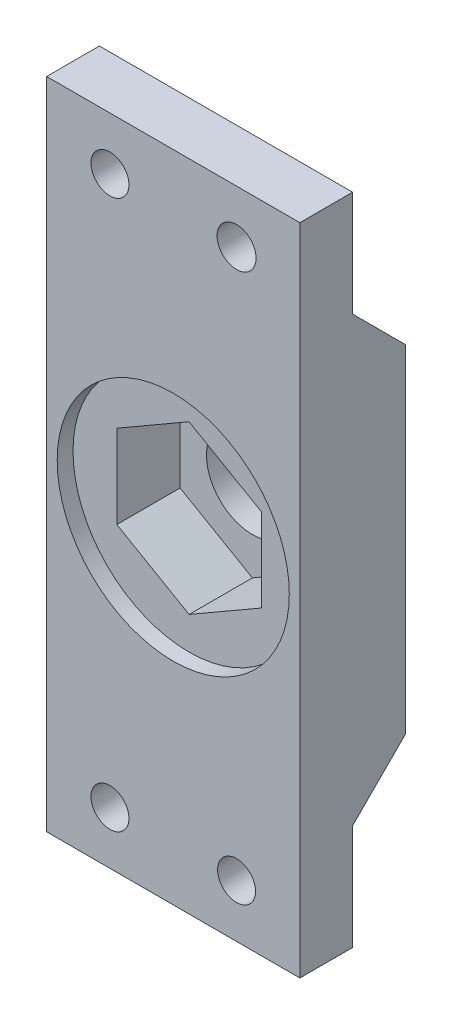
SolidWorks part; units mm, degrees
ref_plane "Plano frontal" through (0, 0, 0) normal (0, 0, 1) x (1, 0, 0)
ref_plane "Plano superior" through (0, 0, 0) normal (0, 1, 0) x (1, 0, 0)
ref_plane "Plano direito" through (0, 0, 0) normal (1, 0, 0) x (0, 0, -1)
sketch "Esboço1" plane through (0, 0, 0) normal (0, 0, 1) x (1, 0, 0)
  line L1 (-12, 31) -> (12, 31)
  line L2 (-12, 31) -> (-12, -31)
  line L3 (-12, -31) -> (12, -31)
  line L4 (12, 31) -> (12, -31)
  line L5 (-12, 31) -> (12, -31) construction
  line L6 (-12, -31) -> (12, 31) construction
  point P0 (0, 0)
extrude "Ressalto-extrusão1" add sketch "Esboço1" along normal blind 10
sketch "Esboço4" plane through (0, 0, 10) normal (0, 0, -1) x (-1, 0, 0)
  circle A0 centre (0, 0) radius 11
extrude "Corte-extrusão1" cut sketch "Esboço4" along normal blind 1.5
sketch "Esboço6" plane through (0, 0, 8.5) normal (0, 0, 1) x (1, 0, 0)
  line L1 (0, -7.9097) -> (6.85, -3.9548)
  line L2 (6.85, -3.9548) -> (6.85, 3.9548)
  line L3 (6.85, 3.9548) -> (0, 7.9097)
  line L4 (0, 7.9097) -> (-6.85, 3.9548)
  line L5 (-6.85, 3.9548) -> (-6.85, -3.9548)
  line L6 (-6.85, -3.9548) -> (0, -7.9097)
  circle A0 centre (0, 0) radius 6.85 construction
extrude "Corte-extrusão2" cut sketch "Esboço6" against normal blind 6
sketch "Esboço9" plane through (0, 0, 10) normal (0, 0, 1) x (1, 0, 0)
  line L0 (0, 31) -> (0, 26) construction
  line L1 (12, 31) -> (-12, 31) construction
  line L2 (0, -31) -> (0, -26) construction
  line L3 (-12, -31) -> (12, -31) construction
  line L4 (0, 26) -> (6, 26) construction
  line L5 (6, 26) -> (-6, 26) construction
  line L6 (-6, 26) -> (-6, -26) construction
  line L7 (-6, -26) -> (6, -26) construction
  circle A0 centre (0, 0) radius 4.35
  circle A1 centre (6, 26) radius 1.85
  circle A2 centre (-6, 26) radius 1.8
  circle A3 centre (-6, -26) radius 1.8
  circle A4 centre (6, -26) radius 1.8
extrude "Corte-extrusão4" cut sketch "Esboço9" against normal through all
sketch "Esboço11" plane through (-12, 0, 0) normal (-1, 0, 0) x (0, 0, 1)
  line L0 (5.0046, -21) -> (5, -31)
  line L1 (0, 31) -> (0, -31) construction
  line L2 (10, -31) -> (0, -31) construction
  line L3 (5, -31) -> (10, -31)
  line L4 (5.0046, -21) -> (0, -15.9954)
  line L5 (0, 15.9954) -> (0, -15.9954)
  line L6 (0, 0) -> (10, 0) construction
  line L8 (10, 31) -> (10, -31)
  line L9 (5.0046, 21) -> (0, 15.9954)
  line L10 (5, 31) -> (10, 31)
  line L11 (5.0046, 21) -> (5, 31)
extrude "Corte-extrusão7" cut sketch "Esboço11" against normal through all flip side to cut
sketch "Esboço12" plane through (0, 0.0023, 5.0141) normal (0, -0.0005, -1) x (-1, 0, 0)
  line L0 (11.7, 21.2977) -> (11.7, 30.6977)
  line L1 (11.7, 30.6977) -> (-11.7, 30.6977)
  line L2 (-11.7, 30.6977) -> (-11.7, 21.2977)
  line L3 (-11.7, 21.2977) -> (11.7, 21.2977)
  line L4 (12, 20.9977) -> (12, 30.9977)
  line L5 (12, 30.9977) -> (-12, 30.9977)
  line L6 (-12, 30.9977) -> (-12, 20.9977)
  line L7 (-12, 20.9977) -> (12, 20.9977)
  line L8 (12, 20.9977) -> (12, 30.9977)
  line L9 (12, 30.9977) -> (-12, 30.9977)
  line L10 (-12, 30.9977) -> (-12, 20.9977)
  line L11 (-12, 20.9977) -> (12, 20.9977)
  line L12 (0, 0) -> (11.7, 0) construction
  line L13 (-12, -20.9977) -> (12, -20.9977)
  line L14 (-12, -30.9977) -> (-12, -20.9977)
  line L15 (12, -30.9977) -> (-12, -30.9977)
  line L16 (12, -20.9977) -> (12, -30.9977)
  line L17 (-11.7, -21.2977) -> (11.7, -21.2977)
  line L18 (-11.7, -30.6977) -> (-11.7, -21.2977)
  line L19 (11.7, -30.6977) -> (-11.7, -30.6977)
  line L20 (11.7, -21.2977) -> (11.7, -30.6977)
  circle A0 centre (-6, 25.9977) radius 1.85 construction
  circle A1 centre (6, 25.9977) radius 1.8 construction
  circle A2 centre (-6, 25.9977) radius 1.85
  circle A3 centre (6, 25.9977) radius 1.8
  circle A4 centre (-6, 25.9977) radius 2.15
  circle A5 centre (6, 25.9977) radius 2.1
  circle A6 centre (6, -25.9977) radius 2.1
  circle A7 centre (-6, -25.9977) radius 2.15
  circle A8 centre (6, -25.9977) radius 1.8
  circle A9 centre (-6, -25.9977) radius 1.85
  ellipse M5 centre (6, 25.9977) end of major axis (6, 24.1977) minor radius 1.8
  line M6 (12, 20.9977) -> (12, 30.9977)
  line M7 (12, 30.9977) -> (-12, 30.9977)
  line M8 (-12, 30.9977) -> (-12, 20.9977)
  line M9 (-12, 20.9977) -> (12, 20.9977)
  ellipse M10 centre (-6, 25.9977) end of major axis (-6, 24.1477) minor radius 1.85
  dimension "D1" = 0
  dimension "D2" = 0.3
  dimension "D3" = 0.3
extrude "suporte" [suppressed] add sketch "Esboço12" along normal up to surface (5.0013 mm away) contours A4 M10 | L3 L2 L1 L0 M9 M6 M7 M8 | A5 M5 | A7 A9 | L16 L13 L14 L15 L17 L20 L19 L18 | A6 A8
